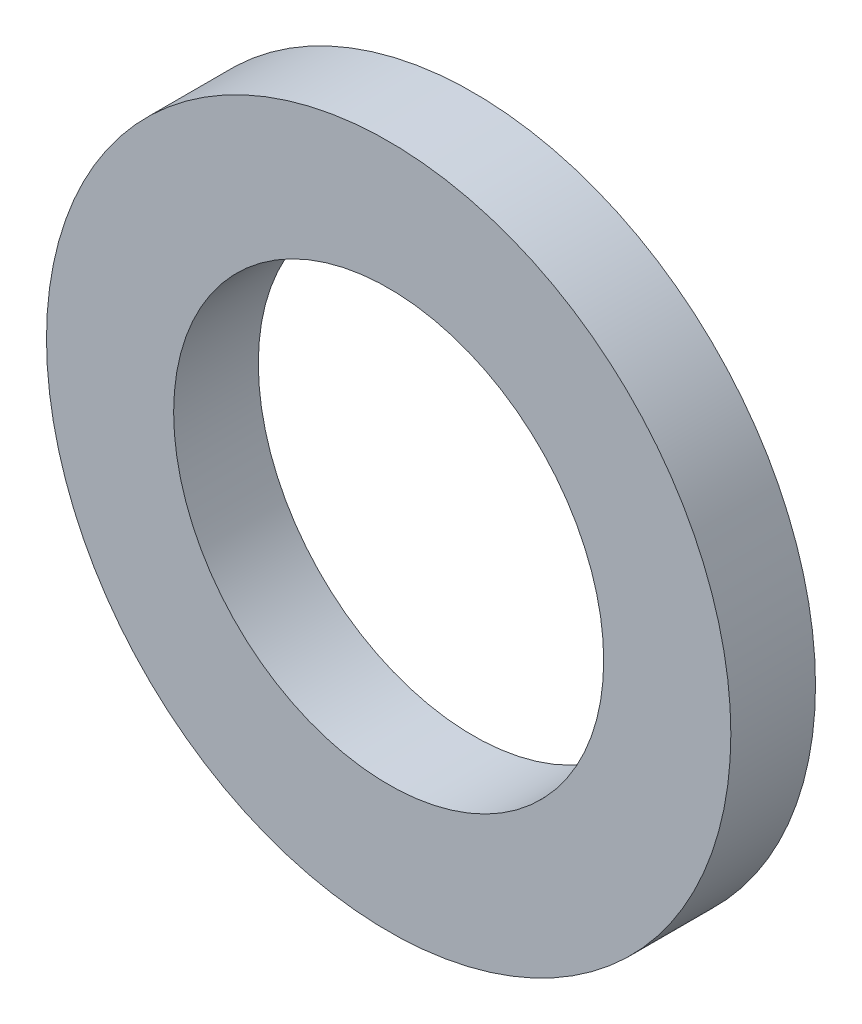
SolidWorks part; units mm, degrees
material "AISI 1020"
ref_plane "Front Plane" through (0, 0, 0) normal (0, 0, 1) x (1, 0, 0)
ref_plane "Top Plane" through (0, 0, 0) normal (0, 1, 0) x (1, 0, 0)
ref_plane "Right Plane" through (0, 0, 0) normal (1, 0, 0) x (0, 0, -1)
sketch "Sketch1" plane through (0, 0, 0) normal (0, 0, 1) x (1, 0, 0)
  circle A0 centre (0, 0) radius 6.365
  circle A1 centre (0, 0) radius 4
  dimension "D1" = 12.73
  dimension "D2" = 8
extrude "Boss-Extrude1" add sketch "Sketch1" along normal blind 1.5748
